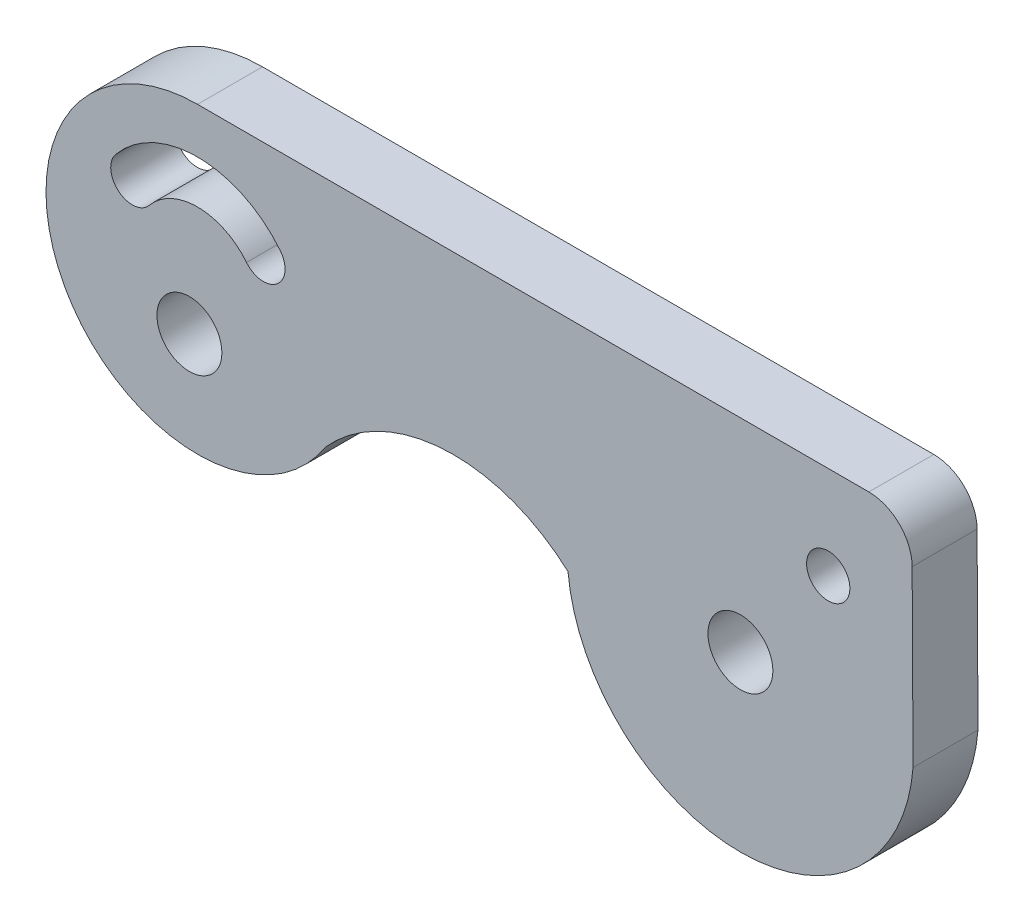
SolidWorks part; units mm, degrees
material "Acrylic (Medium-high impact)"
ref_plane "Front Plane" through (0, 0, 0) normal (0, 0, 1) x (1, 0, 0)
ref_plane "Top Plane" through (0, 0, 0) normal (0, 1, 0) x (1, 0, 0)
ref_plane "Right Plane" through (0, 0, 0) normal (1, 0, 0) x (0, 0, -1)
sketch "Sketch1" plane through (0, 0, 0) normal (0, 0, 1) x (1, 0, 0)
  line L0 (0, 0) -> (31.0105, 0)
  line L1 (33.0526, -10.0038) -> (33.0105, -1.9895)
  line L2 (25.0771, 7.6436) -> (25.0771, -10.1354) construction
  line L3 (25.0771, -9.3774) -> (29.1341, -4.2989) construction
  line L4 (-0.3757, -4.1293) -> (-0.3757, -9.3774) construction
  line L5 (3.0437, -4.5694) -> (-0.3757, -9.3774) construction
  arc A0 (0, 0) -> (5.8951, -10.7747) centre (0, -7) ccw
  arc A1 (5.8951, -10.7747) -> (17.1131, -10.1354) centre (11.8201, -16) cw
  arc A2 (17.1131, -10.1354) -> (33.0526, -10.0038) centre (25.0771, -9.3774) ccw
  arc A3 (31.0105, 0) -> (33.0105, -1.9895) centre (31.0105, -2) cw
  circle A5 centre (25.0771, -9.3774) radius 1.5
  circle A6 centre (29.1341, -4.2989) radius 1
  arc A7 (2.2623, -5.1934) -> (-2.2376, -5.1629) centre (0, -7) ccw
  arc A8 (3.8251, -3.9453) -> (-3.7834, -3.8938) centre (0, -7) ccw
  arc A9 (-3.7834, -3.8938) -> (-2.2376, -5.1629) centre (-3.0105, -4.5284) ccw
  arc A10 (3.8251, -3.9453) -> (2.2623, -5.1934) centre (3.0437, -4.5694) cw
  circle A11 centre (-0.3757, -9.3774) radius 1.5
  point P11 (33, 0)
  dimension "D2" = 7
  dimension "D4" = 7.9
  dimension "D7" = 8
  dimension "D9" = 2
  dimension "D10" = 3
  dimension "D11" = 2
  dimension "D12" = 6.5
  dimension "D14" = 3
  dimension "D15" = 2
  dimension "D16" = 35.42
  dimension "D17" = 4.5
  dimension "D1" = 33
  dimension "D3" = 29
  dimension "D5" = 12.5
  dimension "D6" = 16
  dimension "D8" = 189.927
  dimension "D13" = 38.62
  dimension "D18" = 5.9
extrude "Boss-Extrude1" add sketch "Sketch1" along normal blind 3
